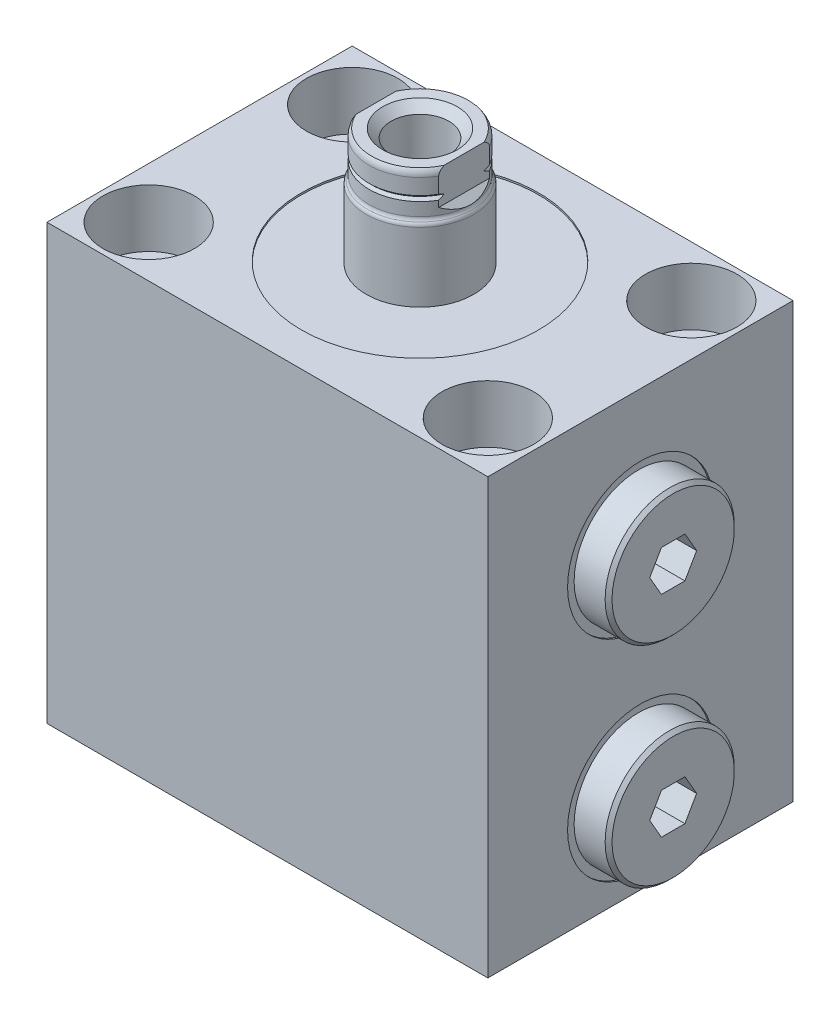
SolidWorks part; units mm, degrees
material "Alloy Steel"
ref_plane "Front Plane" through (0, 0, 0) normal (0, 0, 1) x (1, 0, 0)
ref_plane "Top Plane" through (0, 0, 0) normal (0, 1, 0) x (1, 0, 0)
ref_plane "Right Plane" through (0, 0, 0) normal (1, 0, 0) x (0, 0, -1)
sketch "Sketch1" plane through (0, 0, 0) normal (0, 1, 0) x (1, 0, 0)
  line L0 (-32.5, 22.5) -> (32.5, -22.5) construction
  line L1 (-32.5, 22.5) -> (32.5, 22.5)
  line L2 (-32.5, 22.5) -> (-32.5, -22.5)
  line L3 (-32.5, -22.5) -> (32.5, -22.5)
  line L4 (32.5, 22.5) -> (32.5, -22.5)
  point P4 (0, 0)
  dimension "D1" = 65
  dimension "D2" = 45
extrude "Extrude1" add sketch "Sketch1" along normal blind 64
sketch "Sketch2" plane through (0, 64, 0) normal (0, 1, 0) x (1, 0, 0)
  circle A0 centre (0, 0) radius 17.5
  dimension "D1" = 35
extrude "Cut-Extrude1" cut sketch "Sketch2" against normal blind 0.254
sketch "Sketch3" plane through (0, 0, 0) normal (0, 0, 1) x (1, 0, 0)
  line L0 (-6.848, 44) -> (35.4055, 44) construction
  line L1 (-32.5, 0) -> (32.5, 0) construction
  line L2 (32.5, 44) -> (32.5, 33.256)
  line L3 (32.5, 64) -> (32.5, 0) construction
  line L4 (32.5, 33.256) -> (32.246, 33.256)
  line L5 (32.246, 33.256) -> (32.246, 37.3452)
  line L6 (32.246, 37.3452) -> (31.5348, 38.0564)
  line L7 (31.5348, 38.0564) -> (16.752, 38.0564)
  line L8 (16.752, 38.0564) -> (16.752, 44)
  line L9 (16.752, 44) -> (32.5, 44)
  dimension "D1" = 44
  dimension "D2" = 21.488
  dimension "D3" = 0.254
  dimension "D4" = 11.8872
  dimension "D5" = 15.748
  dimension "D6" = 45
  dimension "D7" = 0.7112
revolve "Cut-Revolve1" cut sketch "Sketch3" angle 360 about L0
sketch "Sketch4" plane through (0, 0, 0) normal (0, 0, 1) x (1, 0, 0)
  line L0 (20.308, 44) -> (20.308, 49.9182)
  line L1 (31.5348, 44) -> (16.752, 44) construction
  line L2 (20.308, 49.9182) -> (32.246, 49.9182)
  line L3 (32.246, 49.9182) -> (32.246, 53.525)
  line L4 (32.246, 53.525) -> (37.326, 53.525)
  line L5 (37.326, 53.525) -> (37.326, 44)
  line L6 (37.326, 44) -> (20.308, 44)
  line L8 (32.246, 33.256) -> (32.246, 54.744) construction
  line L9 (8.7326, 44) -> (38.9701, 44) construction
  dimension "D1" = 11.938
  dimension "D2" = 11.8364
  dimension "D3" = 5.08
  dimension "D4" = 19.05
revolve "Revolve1" add sketch "Sketch4" angle 360 about L9
chamfer "Chamfer1" distance 0.508 angle 45 1 edges at (37.326, 44, 9.525)
sketch "Sketch5" plane through (37.326, 0, 0) normal (1, 0, 0) x (0, 0, -1)
  line L1 (1.7304, 46.9972) -> (-1.7304, 46.9972)
  line L2 (-1.7304, 46.9972) -> (-3.4609, 44)
  line L3 (-3.4609, 44) -> (-1.7304, 41.0028)
  line L4 (-1.7304, 41.0028) -> (1.7304, 41.0028)
  line L5 (1.7304, 41.0028) -> (3.4609, 44)
  line L6 (3.4609, 44) -> (1.7304, 46.9972)
  circle A0 centre (0, 44) radius 2.9972 construction
  dimension "D1" = 5.9944
extrude "Cut-Extrude2" cut sketch "Sketch5" against normal blind 5.9944
pattern_linear "LPattern1" count 2 spacing 31 along (0, -1, 0) of "Cut-Revolve1", "Revolve1", "Chamfer1", "Cut-Extrude2"
sketch "Sketch6" plane through (0, 0, 0) normal (0, 0, 1) x (1, 0, 0)
  line L0 (-32.5, 0) -> (32.5, 0) construction
  line L1 (0, 0) -> (0, 18.7888) construction
  line L12 (0, 0) -> (0, 14.8958)
  line L13 (5.7025, 0) -> (0, 0)
  line L14 (1.2446, 14.148) -> (0, 14.8958)
  line L15 (1.2446, 4.9529) -> (1.2446, 14.148)
  line L16 (1.7525, 4.445) -> (1.2446, 4.9529)
  line L17 (3.2512, 4.445) -> (1.7525, 4.445)
  line L18 (3.2512, 1.448) -> (3.2512, 4.445)
  line L19 (5.7025, 1.448) -> (3.2512, 1.448)
  line L20 (5.7025, 0) -> (5.7025, 1.448)
  dimension "D1" = 59
  dimension "D2" = 14.8958
  dimension "D3" = 2.4892
  dimension "D4" = 11.405
  dimension "D5" = 1.448
  dimension "D6" = 6.5024
  dimension "D7" = 4.445
  dimension "D8" = 45
  dimension "D9" = 0.5079
revolve "Cut-Revolve2" cut sketch "Sketch6" angle 360 about L1
sketch "Sketch7" plane through (0, 0, 0) normal (0, 0, 1) x (1, 0, 0)
  line L0 (0, 0) -> (0, 17.946) construction
  line L1 (0, 14.148) -> (0, 14.8958) construction
  line L2 (-32.5, 0) -> (32.5, 0) construction
  circle A0 centre (4.814, 0.5844) radius 0.889
  dimension "D1" = 9.628
  dimension "D2" = 1.778
  dimension "D3" = 0.5844
revolve "Revolve3" add sketch "Sketch7" angle 360 about L0
pattern_linear "LPattern2" count 2 spacing 25 along (-1, 0, 0) of "Cut-Revolve2", "Revolve3"
sketch "Sketch8" plane through (0, 0, 0) normal (0, 0, 1) x (1, 0, 0)
  line L0 (7.925, 63.746) -> (7.925, 73.9442)
  line L1 (7.1341, 81) -> (0, 81)
  line L2 (0, 81) -> (0, 63.746)
  line L3 (7.5, 80.0094) -> (7.5, 75)
  line L4 (7.925, 63.746) -> (0, 63.746)
  line L5 (0, 0) -> (0, 83.6966) construction
  line L6 (17.5, 63.746) -> (-17.5, 63.746) construction
  line L7 (-32.5, 0) -> (32.5, 0) construction
  arc A0 (7.5, 80.0094) -> (7.1341, 81) centre (5.976, 80.0094) ccw
  arc A1 (7.5, 75) -> (7.7125, 74.4721) centre (8.262, 75) ccw
  arc A2 (7.925, 73.9442) -> (7.7125, 74.4721) centre (7.163, 73.9442) ccw
  dimension "D1" = 1.524
  dimension "D7" = 0.762
  dimension "D8" = 0.762
  dimension "D2" = 6
  dimension "D3" = 81
  dimension "D4" = 0.9906
  dimension "D5" = 15
  dimension "D6" = 15.85
revolve "Revolve4" add sketch "Sketch8" angle 360 about L5
sketch "Sketch10" plane through (0, 0, 0) normal (0, 0, 1) x (1, 0, 0)
  line L0 (5.5, 81) -> (4.267, 79.767)
  line L1 (4.267, 79.767) -> (4.267, 60.68)
  line L2 (4.267, 60.68) -> (0, 58.1161)
  line L3 (0, 58.1161) -> (0, 81)
  line L4 (0, 81) -> (5.5, 81)
  line L5 (0, 81) -> (0, 82.7828) construction
  line L6 (7.1341, 81) -> (-7.1341, 81) construction
  dimension "D1" = 45
  dimension "D2" = 1.233
  dimension "D3" = 8.534
  dimension "D4" = 59
  dimension "D5" = 20.32
revolve "Cut-Revolve3" cut sketch "Sketch10" angle 360 about L5
sketch "Sketch11" plane through (0, 0, 0) normal (0, 0, 1) x (1, 0, 0)
  line L0 (7.5, 77.698) -> (7.119, 77.317)
  line L1 (7.119, 77.317) -> (7.5, 76.936)
  line L2 (7.5, 76.936) -> (7.5, 77.698)
  line L3 (7.5, 75) -> (7.5, 80.0094) construction
  line L4 (7.119, 77.317) -> (7.5, 77.317) construction
  line L5 (7.1341, 81) -> (-7.1341, 81) construction
  line L6 (0, 0) -> (0, 94.5745) construction
  dimension "D1" = 0.762
  dimension "D2" = 3.683
  dimension "D3" = 90
revolve "Cut-Revolve4" cut sketch "Sketch11" angle 360 about L6
sketch "Sketch12" plane through (0, 0, 0) normal (0, 0, 1) x (1, 0, 0)
  line L0 (0, 0) -> (0, 87.4273) construction
  line L1 (6.5, 81) -> (6.5, 76)
  line L2 (5.5, 81) -> (-5.5, 81) construction
  line L3 (6.5, 76) -> (7.925, 74.575)
  line L4 (7.925, 74.575) -> (7.925, 81)
  line L5 (7.925, 81) -> (6.5, 81)
  line L6 (7.925, 63.746) -> (7.925, 73.9442) construction
  line L7 (-7.925, 81) -> (-6.5, 81)
  line L8 (-7.925, 74.575) -> (-7.925, 81)
  line L9 (-6.5, 76) -> (-7.925, 74.575)
  line L10 (-6.5, 81) -> (-6.5, 76)
  dimension "D1" = 13
  dimension "D2" = 45
  dimension "D3" = 5
extrude "Cut-Extrude3" cut sketch "Sketch12" against normal through all and the other way through all
hole_wizard "Hole1" positions "Sketch14" profile "Sketch13" legacy end condition through all
sketch "Sketch14" plane through (0, 64, 0) normal (0, 1, 0) x (-1, 0, 0)
  line L0 (0, 0) -> (0, 30.0241) construction
  line L1 (0, 0) -> (32.2854, 0) construction
  point P0 (25, 15)
  point P10 (25, -15)
  point P12 (-25, -15)
  point P13 (-25, 15)
  dimension "D1" = 30
  dimension "D2" = 50
sketch "Sketch13" plane through (-25, 64, 15) normal (1, 0, 0) x (0, 0, 1)
  line L0 (0, 0) -> (0, 64.3046)
  line L1 (0, 64.3046) -> (4.2545, 64.3046)
  line L2 (4.2545, 64.3046) -> (4.2545, 8.509)
  line L3 (4.2545, 8.509) -> (6.7435, 8.509)
  line L4 (6.7435, 8.509) -> (6.7435, 0)
  line L5 (6.7435, 0) -> (0, 0)
  line L6 (0, 110) -> (0, -10) construction
  dimension "Diameter" = 8.509
  dimension "Depth" = 64.3046
  dimension "C-Bore Diameter" = 13.487
  dimension "C-Bore Depth" = 8.509
